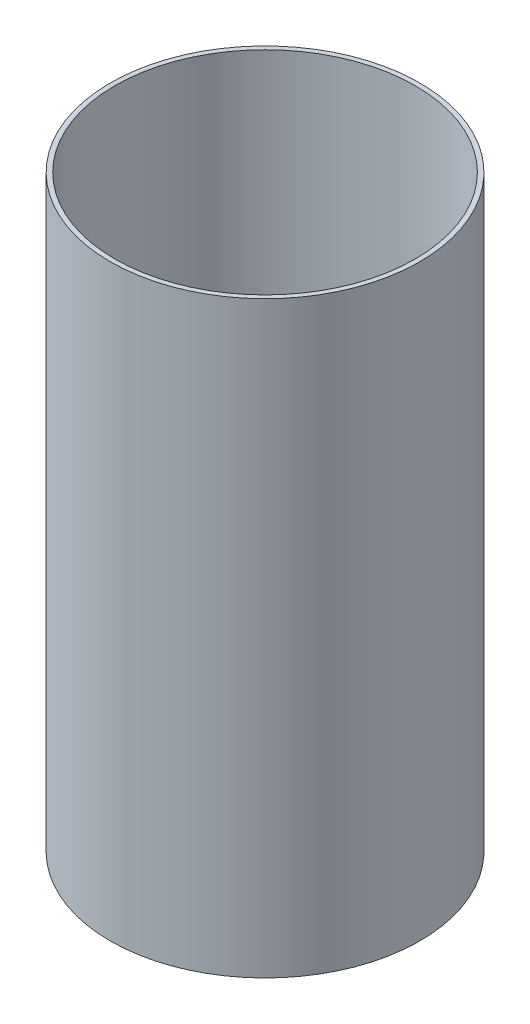
SolidWorks part; units mm, degrees
ref_plane "Front Plane" through (0, 0, 0) normal (0, 0, 1) x (1, 0, 0)
ref_plane "Top Plane" through (0, 0, 0) normal (0, 1, 0) x (1, 0, 0)
ref_plane "Right Plane" through (0, 0, 0) normal (1, 0, 0) x (0, 0, -1)
sketch "Sketch1" plane through (0, 0, 0) normal (0, 1, 0) x (1, 0, 0)
  circle A0 centre (0, 0) radius 63.5
  circle A1 centre (0, 0) radius 61.595
  dimension "D1" = 127
  dimension "D2" = 123.19
extrude "Boss-Extrude1" add sketch "Sketch1" along normal mid plane 241.3
